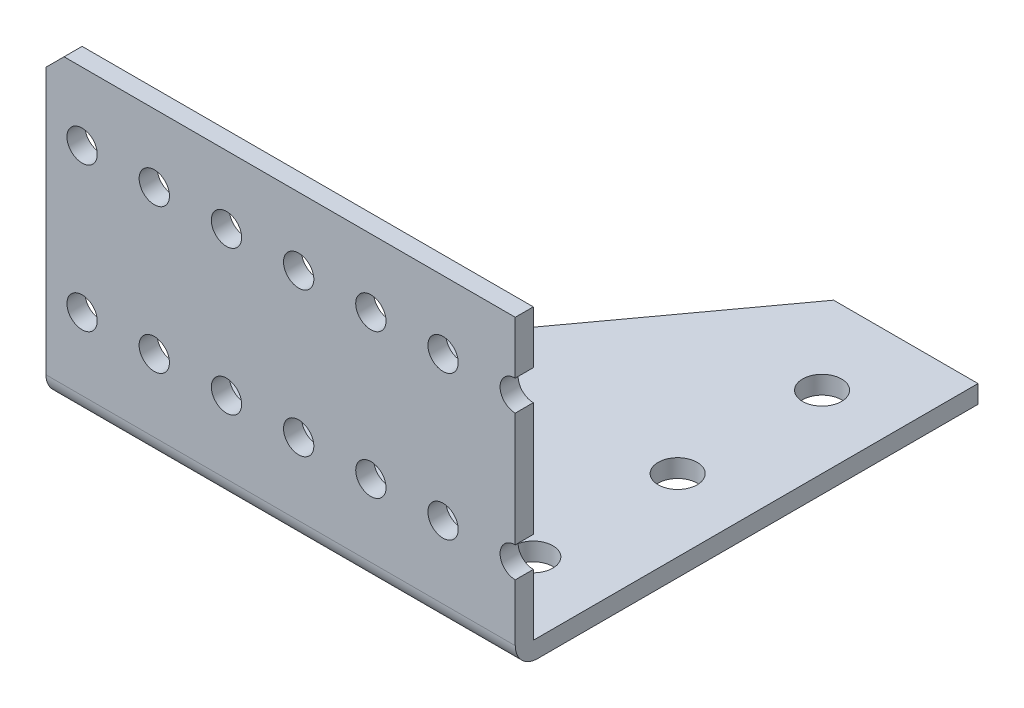
SolidWorks part; units mm, degrees
ref_plane "Front Plane" through (0, 0, 0) normal (0, 0, 1) x (1, 0, 0)
ref_plane "Top Plane" through (0, 0, 0) normal (0, 1, 0) x (1, 0, 0)
ref_plane "Right Plane" through (0, 0, 0) normal (1, 0, 0) x (0, 0, -1)
sketch "Sketch1" plane through (0, 0, 0) normal (0, 1, 0) x (1, 0, 0)
  line L0 (41.275, -40.7035) -> (41.275, 40.7035)
  line L1 (41.275, 40.7035) -> (-41.275, 40.7035)
  line L3 (-41.275, -40.7035) -> (-41.275, 40.7035)
  line L4 (-41.275, -40.7035) -> (41.275, -40.7035)
  line L5 (41.275, 40.7035) -> (-41.275, -40.7035) construction
  line L6 (0, -55) -> (0, 55) construction
  line L7 (-55, 0) -> (55, 0) construction
  point P2 (0, 0)
  dimension "D2" = 81.407
  dimension "D1" = 82.55
extrude "Boss-Extrude1" add sketch "Sketch1" along normal blind 3.175 from offset 34.925 offset against normal yes
sketch "Sketch3" plane through (0, -31.75, 0) normal (0, 1, 0) x (1, 0, 0)
  line L0 (41.275, -40.7035) -> (-41.275, -40.7035)
  line L1 (-41.275, -40.7035) -> (-41.275, -37.5285)
  line L2 (-41.275, -37.5285) -> (41.275, -37.5285)
  line L3 (-41.275, -40.7035) -> (41.275, -40.7035) construction
  line L4 (41.275, -40.7035) -> (41.275, -37.5285)
  line L5 (-41.275, 40.7035) -> (-41.275, -40.7035) construction
  line L6 (41.275, -40.7035) -> (41.275, 40.7035) construction
  dimension "D1" = 3.175
extrude "Boss-Extrude2" add sketch "Sketch3" along normal blind 50.8
hole_wizard "#10 Clearance Hole2" positions "Sketch7" profile "Sketch6" hole size "#10" standard "ANSI Inch" end condition through all
sketch "Sketch7" plane through (0, 0, -40.7035) normal (0, 0, -1) x (-1, 0, 0)
  line L2 (-41.275, -18.288) -> (34.925, -18.288) construction
  line L5 (-41.275, 7.112) -> (34.925, 7.112) construction
  line L8 (41.275, 19.05) -> (41.275, -31.75) construction
  line L9 (-41.275, 19.05) -> (-41.275, -31.75) construction
  line L10 (-41.275, 19.05) -> (41.275, 19.05) construction
  point P56 (22.225, 7.112)
  point P57 (9.525, 7.112)
  point P58 (-3.175, 7.112)
  point P59 (-15.875, 7.112)
  point P61 (-28.575, 7.112)
  point P118 (22.225, -18.288)
  point P119 (9.525, -18.288)
  point P120 (-3.175, -18.288)
  point P121 (-15.875, -18.288)
  point P123 (-28.575, -18.288)
  point P157 (34.925, 7.112)
  point P159 (34.925, -18.288)
  point P185 (-41.275, 7.112)
  point P189 (-41.275, -18.288)
  dimension "D1" = 6.35
  dimension "D2" = 11.938
  dimension "D3" = 12.7
  dimension "D4" = 25.4
  dimension "D5" = 12.7
  dimension "D6" = 12.7
  dimension "D7" = 12.7
  dimension "D8" = 12.7
  dimension "D10" = 12.7
sketch "Sketch6" plane through (-22.225, 7.112, -40.7035) normal (1, 0, 0) x (0, 1, 0)
  line L0 (0, 0) -> (0, 81.407)
  line L1 (0, 81.407) -> (2.667, 81.407)
  line L2 (2.667, 81.407) -> (2.667, 0)
  line L5 (2.667, 0) -> (0, 0)
  line L11 (0, -6.35) -> (0, 107.95) construction
  dimension "Thru Hole Dia." = 5.334
  dimension "Thru Hole Depth" = 81.407
chamfer "Chamfer1" distance 3.175 angle 45 1 edges at (-41.275, 19.05, 39.116)
fillet "Fillet2" radius 3.937 1 edges at (0, -34.925, 40.7035)
sketch "Sketch9" plane through (0, -34.925, 0) normal (0, -1, 0) x (1, 0, 0)
  line L0 (-41.275, 37.5285) -> (15.875, -40.7035)
  line L1 (-41.275, -40.7035) -> (-41.275, 36.7665) construction
  line L2 (41.275, -40.7035) -> (-41.275, -40.7035) construction
  line L3 (41.275, 36.7665) -> (41.275, -40.7035) construction
  line L4 (15.875, -40.7035) -> (-41.275, -40.7035)
  line L5 (-41.275, -40.7035) -> (-41.275, 37.5285)
  line L6 (-41.275, 40.7035) -> (41.275, 40.7035) construction
  line L7 (28.575, -40.7035) -> (28.575, 36.7665) construction
  line L8 (41.275, 36.7665) -> (-41.275, 36.7665) construction
  line L9 (41.275, 37.5285) -> (-41.275, 37.5285) construction
  circle A0 centre (34.925, 23.9395) radius 3.429 construction
  circle A1 centre (34.925, 11.2395) radius 3.429 construction
  circle A2 centre (34.925, -1.4605) radius 3.429 construction
  circle A3 centre (28.575, 24.8285) radius 3.429
  circle A7 centre (28.575, -0.5715) radius 3.429
  circle A8 centre (28.575, -25.9715) radius 3.429
  dimension "D3" = 6.858
  dimension "D7" = 16.764
  dimension "D9" = 6.858
  dimension "D10" = 12.7
  dimension "D11" = 3
  dimension "D12" = 25.4
  dimension "D1" = 25.4
  dimension "D2" = 0
  dimension "D4" = 12.7
  dimension "D5" = 12.7
  dimension "D6" = 6.35
  dimension "D8" = 12.7
extrude "Cut-Extrude2" cut sketch "Sketch9" against normal through all
